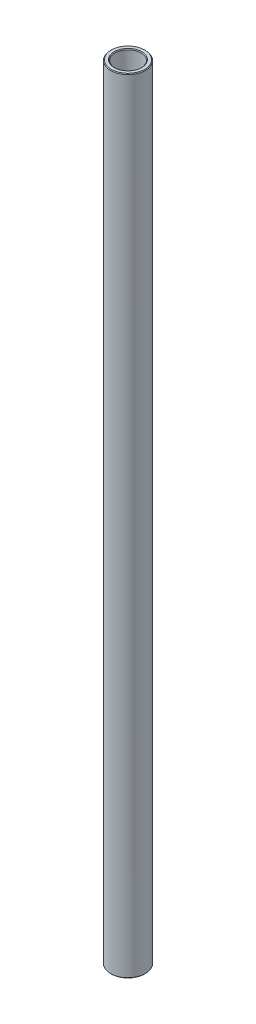
SolidWorks part; units mm, degrees
ref_plane "Front Plane" through (0, 0, 0) normal (0, 0, 1) x (1, 0, 0)
ref_plane "Top Plane" through (0, 0, 0) normal (0, 1, 0) x (1, 0, 0)
ref_plane "Right Plane" through (0, 0, 0) normal (1, 0, 0) x (0, 0, -1)
sketch "Sketch1" plane through (0, 0, 0) normal (0, 0, 1) x (1, 0, 0)
  line L0 (0, 11.6086) -> (0, -11.6086) construction
  line L1 (4.7625, 142.875) -> (6.35, 142.875)
  line L2 (6.35, 142.875) -> (6.35, -142.875)
  line L3 (6.35, -142.875) -> (4.7625, -142.875)
  line L4 (4.7625, -142.875) -> (4.7625, 142.875)
  line L5 (4.7625, 0) -> (0, 0) construction
  dimension "D1" = 9.525
  dimension "D2" = 12.7
  dimension "D3" = 285.75
revolve "Revolve1" add sketch "Sketch1" angle 360 about L0
chamfer "Chamfer1" distance 0.254 angle 45 4 edges at (-4.7625, -142.875, 0) (-6.35, -142.875, 0) (-6.35, 142.875, 0) (-4.7625, 142.875, 0)
